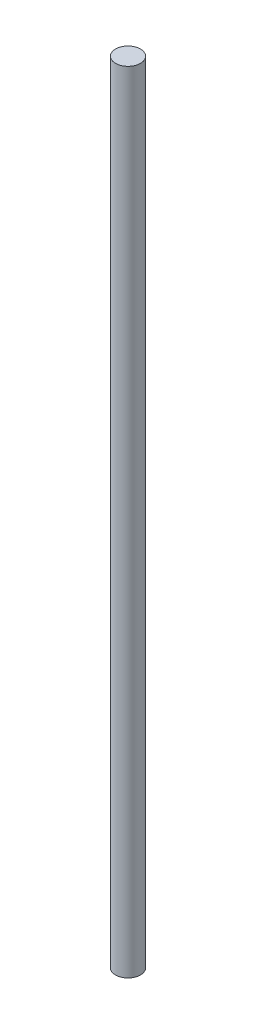
SolidWorks part; units mm, degrees
ref_plane "Front Plane" through (0, 0, 0) normal (0, 0, 1) x (1, 0, 0)
ref_plane "Top Plane" through (0, 0, 0) normal (0, 1, 0) x (1, 0, 0)
ref_plane "Right Plane" through (0, 0, 0) normal (1, 0, 0) x (0, 0, -1)
sketch "Sketch1" plane through (0, 0, 0) normal (0, 1, 0) x (1, 0, 0)
  circle A0 centre (0, 0) radius 4.6609
  dimension "D1" = 9.3218
extrude "Boss-Extrude1" add sketch "Sketch1" along normal blind 295.275
